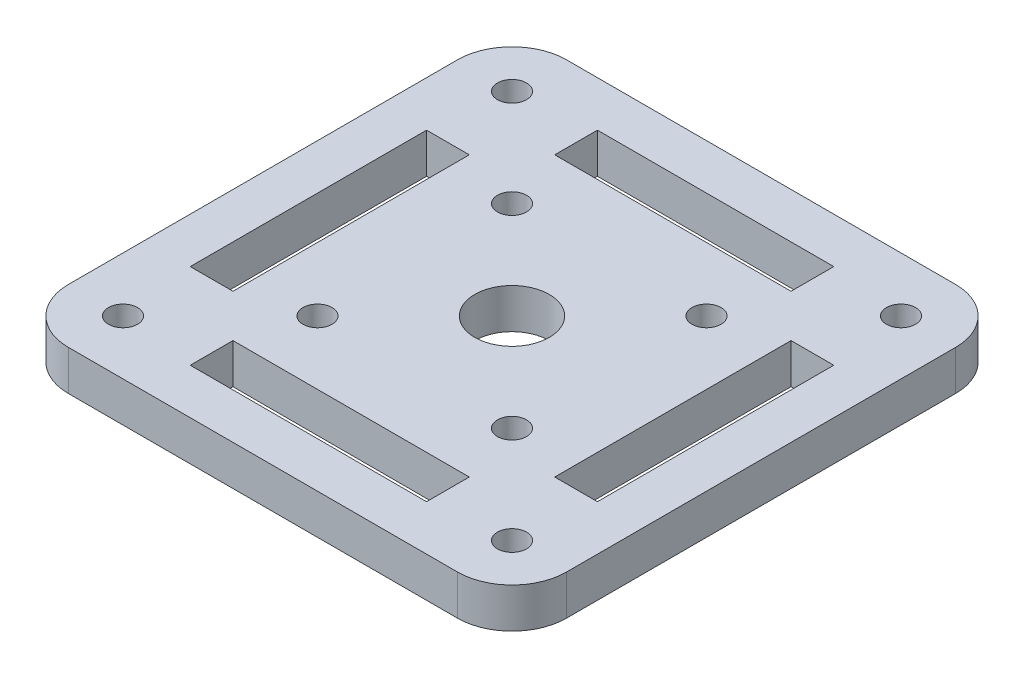
SolidWorks part; units mm, degrees
ref_plane "前视基准面" through (0, 0, 0) normal (0, 0, 1) x (1, 0, 0)
ref_plane "上视基准面" through (0, 0, 0) normal (0, 1, 0) x (1, 0, 0)
ref_plane "右视基准面" through (0, 0, 0) normal (1, 0, 0) x (0, 0, -1)
sketch "草图1" plane through (0, 0, 0) normal (0, 1, 0) x (1, 0, 0)
  line L0 (0, 0) -> (27.4, 27.4) construction
  line L1 (-27.4, 27.4) -> (27.4, 27.4)
  line L2 (-27.4, 27.4) -> (-27.4, -27.4)
  line L3 (-27.4, -27.4) -> (27.4, -27.4)
  line L4 (27.4, 27.4) -> (27.4, -27.4)
  line L5 (0, -27.4) -> (0, 27.4) construction
  line L6 (-27.4, 0) -> (27.4, 0) construction
  line L7 (17.7, -5) -> (17.7, 5)
  line L8 (17.7, 5) -> (22.4, 5) construction
  line L9 (22.4, 5) -> (22.4, -5)
  line L10 (17.7, 5) -> (17.7, 13)
  line L11 (17.7, 13) -> (22.4, 13)
  line L12 (22.4, 13) -> (22.4, 5)
  line L13 (0, 0) -> (27.4, -27.4) construction
  line L14 (22.4, -13) -> (22.4, -5)
  line L15 (17.7, -13) -> (22.4, -13)
  line L16 (17.7, -5) -> (17.7, -13)
  line L17 (17.7, -5) -> (22.4, -5) construction
  line L18 (-5, 17.7) -> (-5, 22.4) construction
  line L19 (5, 17.7) -> (5, 22.4) construction
  line L20 (-5, 17.7) -> (-13, 17.7)
  line L21 (-13, 17.7) -> (-13, 22.4)
  line L22 (-13, 22.4) -> (-5, 22.4)
  line L23 (13, 22.4) -> (5, 22.4)
  line L24 (13, 17.7) -> (13, 22.4)
  line L25 (5, 17.7) -> (13, 17.7)
  line L26 (5, 22.4) -> (-5, 22.4)
  line L27 (-5, 17.7) -> (5, 17.7)
  line L28 (0, 0) -> (-27.4, -27.4) construction
  line L29 (0, 0) -> (-27.4, 27.4) construction
  line L30 (5, -17.7) -> (5, -22.4) construction
  line L31 (-5, -17.7) -> (-5, -22.4) construction
  line L32 (5, -17.7) -> (13, -17.7)
  line L33 (13, -17.7) -> (13, -22.4)
  line L34 (13, -22.4) -> (5, -22.4)
  line L35 (-13, -22.4) -> (-5, -22.4)
  line L36 (-13, -17.7) -> (-13, -22.4)
  line L37 (-5, -17.7) -> (-13, -17.7)
  line L38 (-5, -22.4) -> (5, -22.4)
  line L39 (5, -17.7) -> (-5, -17.7)
  line L40 (-17.7, -5) -> (-22.4, -5) construction
  line L41 (-17.7, 5) -> (-22.4, 5) construction
  line L42 (-17.7, 5) -> (-17.7, -5)
  line L43 (-22.4, -5) -> (-22.4, 5)
  line L44 (-17.7, -5) -> (-17.7, -13)
  line L45 (-17.7, -13) -> (-22.4, -13)
  line L46 (17.7, 13) -> (17.7, 17.7) construction
  line L47 (-22.4, -13) -> (-22.4, -5)
  line L48 (-22.4, 13) -> (-22.4, 5)
  line L49 (-17.7, 13) -> (-22.4, 13)
  line L50 (-17.7, 5) -> (-17.7, 13)
  circle A0 centre (0, 0) radius 4.1
  circle A1 centre (21.4, 21.4) radius 1.6
  circle A2 centre (21.4, -21.4) radius 1.6
  circle A3 centre (-21.4, -21.4) radius 1.6
  circle A4 centre (-21.4, 21.4) radius 1.6
  point P17 (22.4, 0)
  point P18 (17.7, 0)
  point P32 (0, 17.7)
  point P33 (0, 22.4)
  point P42 (0, -17.7)
  point P43 (0, -22.4)
  point P53 (-22.4, 0)
  point P54 (-17.7, 0)
  dimension "D1" = 8.2
  dimension "D8" = 3.2
  dimension "D2" = 45
  dimension "D3" = 4.7
  dimension "D5" = 5
  dimension "D6" = 8
  dimension "D7" = 5
  dimension "D9" = 6
extrude "凸台-拉伸1" add sketch "草图1" along normal blind 4.4
fillet "圆角1" radius 6 4 edges at (-27.4, 2.2, 27.4) (-27.4, 2.2, -27.4) (27.4, 2.2, -27.4) (27.4, 2.2, 27.4)
sketch "草图2" plane through (0, 4.4, 0) normal (0, 1, 0) x (1, 0, 0)
  line L0 (0, 0) -> (21.4, 21.4) construction
  circle A0 centre (10.7, 10.7) radius 1.6
  circle A1 centre (10.7, -10.7) radius 1.6
  circle A2 centre (-10.7, -10.7) radius 1.6
  circle A3 centre (-10.7, 10.7) radius 1.6
  point P15 (0, 0)
  dimension "D1" = 3.2
  dimension "D2" = 4
extrude "切除-拉伸1" cut sketch "草图2" against normal blind 10
